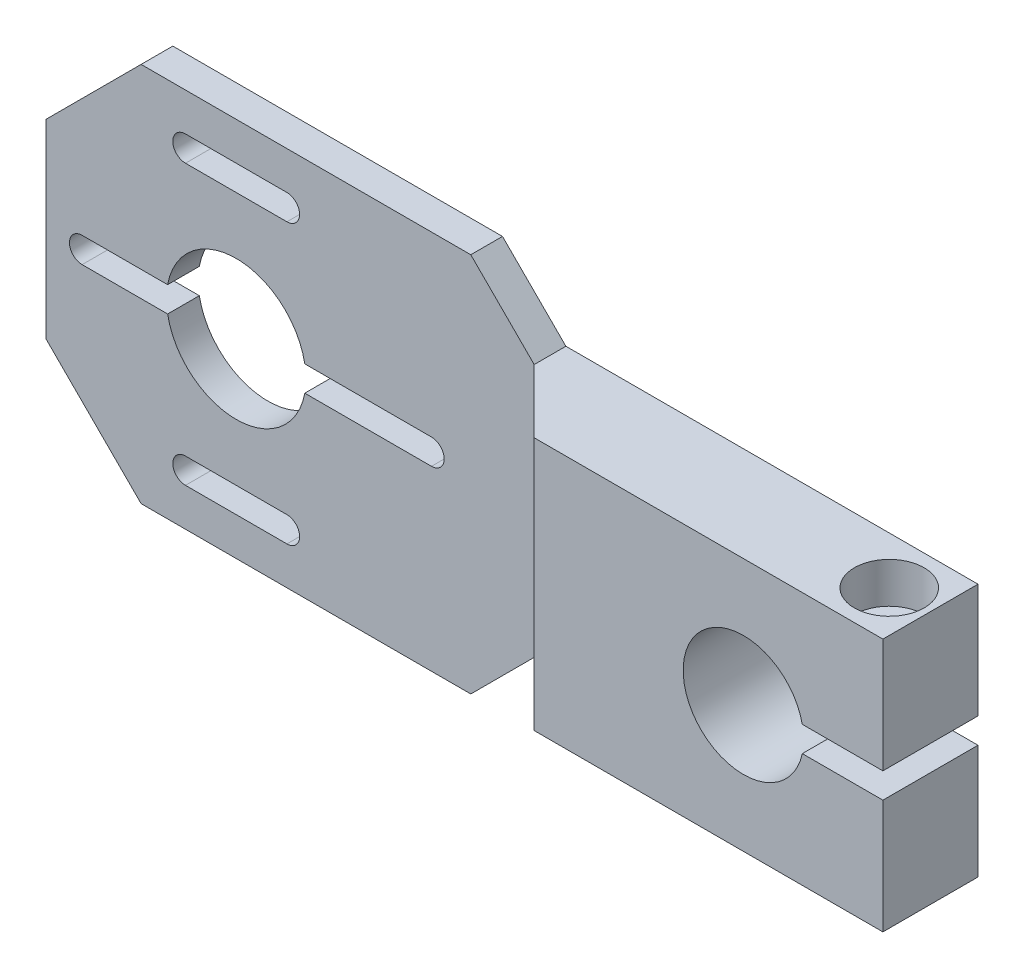
SolidWorks part; units mm, degrees
material "7075-T6, Plaque (SS)"
ref_plane "Plan de face" through (0, 0, 0) normal (0, 0, 1) x (1, 0, 0)
ref_plane "Plan de dessus" through (0, 0, 0) normal (0, 1, 0) x (1, 0, 0)
ref_plane "Plan de droite" through (0, 0, 0) normal (1, 0, 0) x (0, 0, -1)
sketch "Esquisse1" plane through (0, 0, 0) normal (0, 0, 1) x (1, 0, 0)
  line L0 (0, 0) -> (78.0757, 0) construction
  line L1 (0, 0) -> (0, -42) construction
  line L2 (24.8181, 0) -> (158.871, 0) construction
  line L3 (37, 30) -> (47, 20)
  line L4 (37, 30) -> (-15, 30)
  line L5 (37, -30) -> (47, -20)
  line L6 (90, 0) -> (125.9239, 0) construction
  line L7 (112, 20) -> (112, 2)
  line L8 (-30, 15) -> (-30, -15)
  line L9 (112, 2) -> (99.2871, 2)
  line L10 (112, -2) -> (99.2871, -2)
  line L11 (112, 20) -> (47, 20)
  line L12 (-15, -30) -> (37, -30)
  line L13 (-15, 30) -> (-30, 15)
  line L14 (-30, -15) -> (-15, -30)
  line L15 (0, 0) -> (0, 44) construction
  line L19 (-8, 22) -> (8, 22) construction
  line L20 (-8, 24) -> (8, 24)
  line L21 (-8, 20) -> (8, 20)
  line L22 (-8, -22) -> (8, -22) construction
  line L23 (-8, -24) -> (8, -24)
  line L24 (-8, -20) -> (8, -20)
  line L26 (112, -20) -> (112, -2)
  line L27 (112, -20) -> (47, -20)
  circle A0 centre (0, 0) radius 11
  arc A5 (99.2871, 2) -> (99.2871, -2) centre (90, 0) ccw
  circle A6 centre (0, 0) radius 29.5 construction
  arc A13 (-8, 24) -> (-8, 20) centre (-8, 22) ccw
  arc A14 (8, 20) -> (8, 24) centre (8, 22) ccw
  arc A15 (-8, -24) -> (-8, -20) centre (-8, -22) cw
  arc A16 (8, -20) -> (8, -24) centre (8, -22) cw
  point P3 (-30, -30)
  point P7 (-30, 30)
  point P54 (0, 22)
  point P62 (0, -22)
  point P79 (112, 20)
  point P81 (112, -20)
  dimension "D3" = 22
  dimension "D4" = 16
  dimension "D15" = 2
  dimension "D16" = 4
  dimension "D28" = 90
  dimension "D9" = 9.5
  dimension "D7" = 142
  dimension "D12" = 59
  dimension "D5" = 60
  dimension "D8" = 22
  dimension "D10" = 65
  dimension "D6" = 45
  dimension "D20" = 40
  dimension "D23" = 22
extrude "Boss.-Extru.1" add sketch "Esquisse1" along normal blind 15
hole_wizard "Chambrage pour vis à tête hexagonale M61" positions "Esquisse2" profile "Esquisse3" counterbore size "M6" standard "ISO" end condition up to next
sketch "Esquisse2" plane through (0, 20, 0) normal (0, -1, 0) x (-1, 0, 0)
  line L9 (-112, -7.5) -> (-157.4079, -7.5) construction
  line L10 (-112, -15) -> (-112, 0) construction
  point P0 (-105.5, -7.5)
  dimension "D1" = 6.5
sketch "Esquisse3" plane through (105.5, 20, 7.5) normal (1, 0, 0) x (0, 0, 1)
  line L0 (0, 0) -> (0, 18)
  line L1 (0, 18) -> (3.3, 18)
  line L3 (3.3, 18) -> (3.3, 6.4)
  line L4 (3.3, 6.4) -> (5.5, 6.4)
  line L5 (5.5, 6.4) -> (5.5, 0)
  line L7 (5.5, 0) -> (0, 0)
  line L11 (0, -6.35) -> (0, 107.95) construction
  dimension "Diamètre du perçage jusqu'au prochain" = 6.6
  dimension "Profondeur du perçage jusqu'au prochain" = 18
  dimension "Diamètre du chambrage" = 11
  dimension "Profondeur du chambrage" = 6.4
ref_plane "Plan1" through (0, 60, 0) normal (0, 1, 0) x (1, 0, 0)
sketch "Esquisse4" plane through (0, 60, 0) normal (0, 1, 0) x (1, 0, 0)
  line L0 (-30, -5) -> (47, -5)
  line L1 (47, -5) -> (80.8687, -38.8687)
  line L2 (-30, -38.8687) -> (80.8687, -38.8687)
  line L3 (-30, -38.8687) -> (-30, -5)
  line L5 (37, 0) -> (-15, 0) construction
  line L7 (47, -15) -> (47, 0) construction
  line L8 (-30, -15) -> (-30, 0) construction
  dimension "D1" = 45
  dimension "D2" = 5
extrude "Enlèv. mat.-Extru.7" cut sketch "Esquisse4" against normal through all
hole_wizard "Trou taraudé M61" positions "Esquisse5" profile "Esquisse6" tap size "M6" standard "ISO" end condition through all
sketch "Esquisse5" plane through (0, -2, 0) normal (0, 1, 0) x (1, 0, 0)
  line L4 (112, -7.5) -> (99, -7.5) construction
  line L5 (112, -15) -> (112, 0) construction
  point P0 (105.5, -7.5)
  dimension "D1" = 6.5
sketch "Esquisse6" plane through (105.5, -2, 7.5) normal (1, 0, 0) x (0, 0, 1)
  line L0 (0, 0) -> (0, 28)
  line L1 (0, 28) -> (2.5, 28)
  line L2 (2.5, 28) -> (2.5, 0)
  line L5 (2.5, 0) -> (0, 0)
  line L11 (0, -6.35) -> (0, 107.95) construction
  dimension "Diamètre du trou pour taraudage jusqu'au prochain" = 5
  dimension "Profondeur du trou pour taraudage jusqu'au prochain" = 28
cosmetic thread "Filetage de perçage1" parameters "D2"=6
sketch "Esquisse7" plane through (0, 0, 5) normal (0, 0, 1) x (1, 0, 0)
  line L0 (-24.3, 0) -> (-6.3, 0) construction
  line L1 (-24.3, 2) -> (-6.3, 2)
  line L2 (-24.3, -2) -> (-6.3, -2)
  line L3 (8.8, 0) -> (30.8, 0) construction
  line L4 (8.8, 2) -> (30.8, 2)
  line L5 (8.8, -2) -> (30.8, -2)
  line L6 (0, 0) -> (0, 20) construction
  line L7 (-8, 20) -> (8, 20) construction
  arc A0 (-24.3, 2) -> (-24.3, -2) centre (-24.3, 0) ccw
  arc A1 (-6.3, -2) -> (-6.3, 2) centre (-6.3, 0) ccw
  arc A2 (8.8, 2) -> (8.8, -2) centre (8.8, 0) ccw
  arc A3 (30.8, -2) -> (30.8, 2) centre (30.8, 0) ccw
  point P3 (-15.3, 0)
  point P8 (19.8, 0)
  dimension "D1" = 2
  dimension "D2" = 22
  dimension "D3" = 30.8
  dimension "D4" = 18
  dimension "D5" = 24.3
extrude "Enlèv. mat.-Extru.8" cut sketch "Esquisse7" against normal through all
